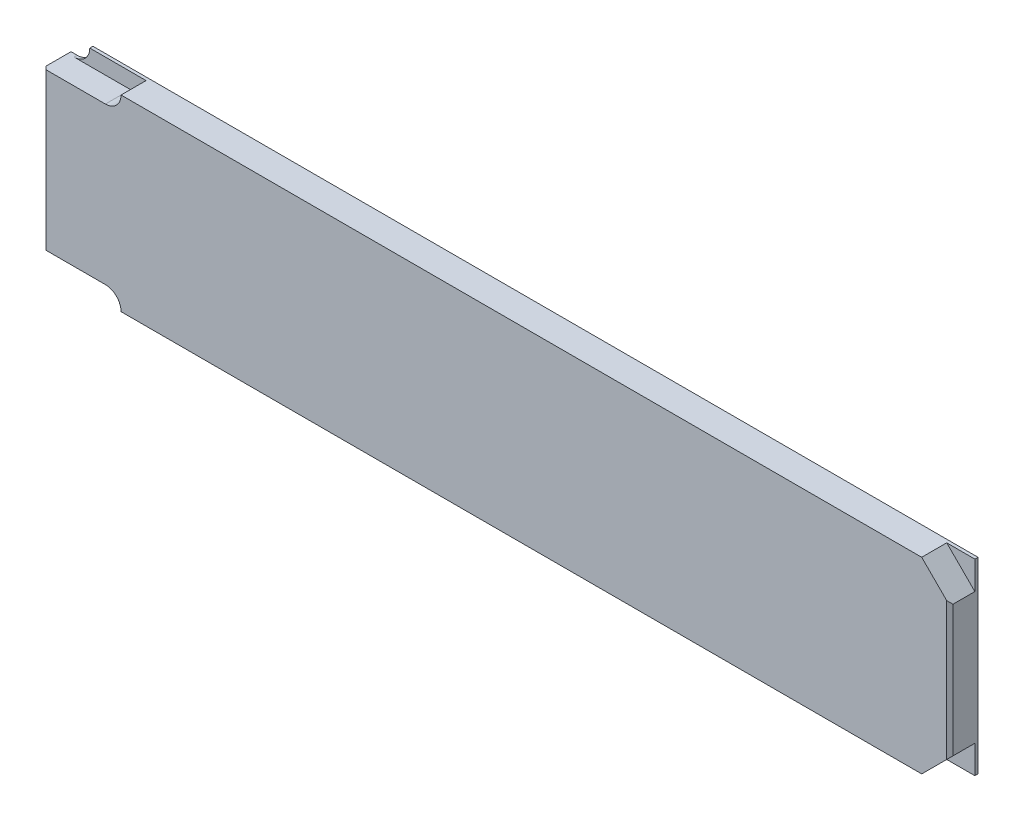
SolidWorks part; units mm, degrees
ref_plane "Plane1" through (0, 0, 0) normal (0, 0, 1) x (1, 0, 0)
ref_plane "Plane2" through (0, 0, 0) normal (0, 1, 0) x (1, 0, 0)
ref_plane "Plane3" through (0, 0, 0) normal (1, 0, 0) x (0, 0, -1)
sketch "Sketch1" plane through (0, 0, 0) normal (0, 0, 1) x (1, 0, 0)
  line L0 (7, 0) -> (290, 0)
  line L1 (0, 5) -> (0, 55)
  line L2 (290, 60) -> (7, 60)
  line L3 (290, 60) -> (290, 0)
  line L4 (0, 5) -> (2, 5)
  line L8 (-4.3217, 30) -> (77.779, 30) construction
  line L10 (0, 55) -> (2, 55)
  arc A0 (2, 5) -> (7, 0) centre (2, 0) cw
  arc A1 (2, 55) -> (7, 60) centre (2, 60) ccw
  dimension "D4" = 5
  dimension "D1" = 290
  dimension "D2" = 7
  dimension "D3" = 60
  dimension "D5" = 5
extrude "Base-Extrude" add sketch "Sketch1" along normal blind 9
sketch "Sketch2" plane through (0, 0, 9) normal (0, 0, 1) x (1, 0, 0)
  line L0 (0, 30) -> (290, 30) construction
  line L1 (7, 0) -> (290, 0) construction
  line L2 (2, 5) -> (20, 5)
  line L3 (290, 60) -> (290, 0) construction
  line L4 (145, 30) -> (145, -44) construction
  line L6 (290, 60) -> (290, 0) construction
  line L7 (25, 0) -> (7, 0)
  line L8 (290, 60) -> (290, 51)
  line L9 (290, 9) -> (281, 0)
  line L10 (290, 51) -> (281, 60)
  line L11 (290, 60) -> (7, 60) construction
  line L12 (290, 60) -> (281, 60)
  line L13 (290, 9) -> (290, 0)
  line L14 (281, 0) -> (290, 0)
  line L18 (25, 60) -> (7, 60)
  line L21 (2, 55) -> (20, 55)
  arc A0 (20, 5) -> (25, 0) centre (20, 0) cw
  arc A2 (7, 0) -> (2, 5) centre (2, 0) ccw construction
  arc A3 (7, 0) -> (2, 5) centre (2, 0) ccw
  arc A4 (7, 60) -> (2, 55) centre (2, 60) cw
  arc A5 (20, 55) -> (25, 60) centre (20, 60) ccw
  dimension "D4" = 25
  dimension "D1" = 5
  dimension "D2" = 45
  dimension "D3" = 9
extrude "Cut-Extrude1" cut sketch "Sketch2" against normal offset from surface (8 mm away) 1 up to face at (75.0089, 30, 0)
chamfer "Chamfer1" distance 1 angle 45 2 edges at (0, 30, 9) (290, 30, 9)
sketch "Sketch3" plane through (0, 0, 0) normal (0, 0, -1) x (-1, 0, 0)
  text T0 "63761" font "Century Gothic" height 12.7
extrude "Cut-Extrude2" cut sketch "Sketch3" against normal blind 0.13
